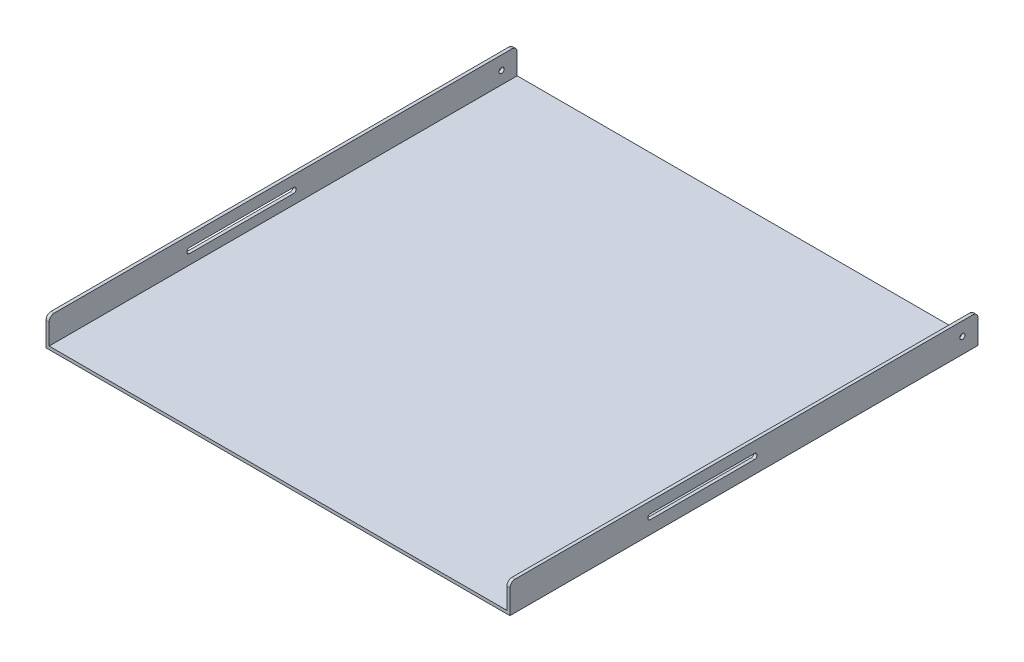
SolidWorks part; units mm, degrees
ref_plane "Front Plane" through (0, 0, 0) normal (0, 0, 1) x (1, 0, 0)
ref_plane "Top Plane" through (0, 0, 0) normal (0, 1, 0) x (1, 0, 0)
ref_plane "Right Plane" through (0, 0, 0) normal (1, 0, 0) x (0, 0, -1)
sketch "Sketch1" plane through (0, 0, 0) normal (0, 0, 1) x (1, 0, 0)
  line L0 (-250, 50) -> (-250, 0)
  line L1 (-250, 0) -> (630, 0)
  line L2 (630, 0) -> (630, 50)
  dimension "D1" = 880
  dimension "D2" = 250
  dimension "D3" = 50
  dimension "D4" = 50
extrude "Extrude-Thin1" add sketch "Sketch1" along normal mid plane 900 thin
sketch "Sketch2" plane through (636, 0, 0) normal (1, 0, 0) x (0, 0, -1)
  line L0 (20, 24) -> (-180, 24) construction
  line L1 (20, 19) -> (-180, 19)
  line L2 (20, 29) -> (-180, 29)
  circle A0 centre (420, 24) radius 5
  arc A1 (20, 19) -> (20, 29) centre (20, 24) ccw
  arc A2 (-180, 29) -> (-180, 19) centre (-180, 24) ccw
  point P4 (-80, 24)
  dimension "D1" = 10
  dimension "D2" = 30
  dimension "D3" = 30
  dimension "D4" = 80
  dimension "D5" = 200
  dimension "D6" = 10
extrude "Cut-Extrude1" cut sketch "Sketch2" against normal through all
fillet "Fillet1" radius 10 4 edges at (-253, 50, -450) (633, 50, -450) (-253, 50, 450) (633, 50, 450)
